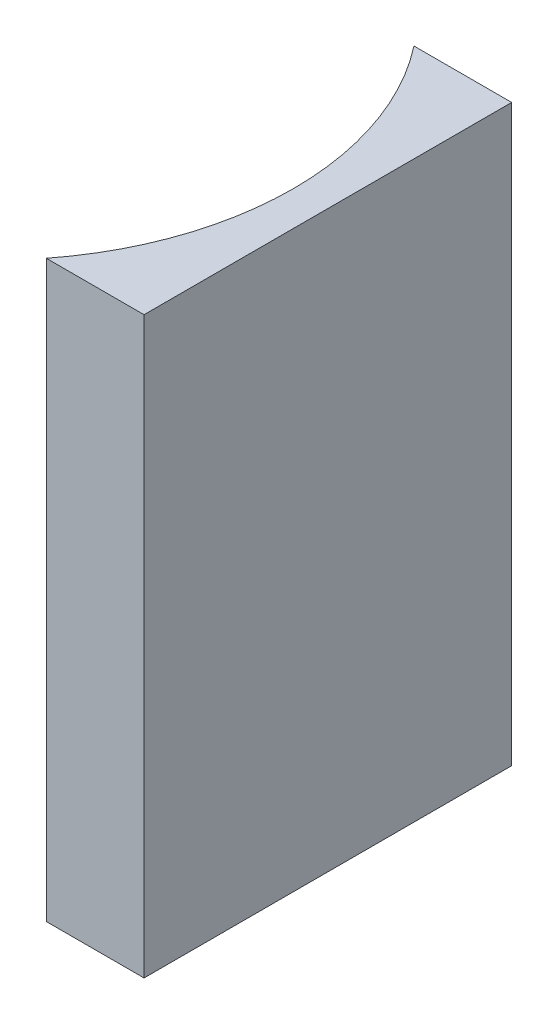
SolidWorks part; units mm, degrees
ref_plane "前视基准面" through (0, 0, 0) normal (0, 0, 1) x (1, 0, 0)
ref_plane "上视基准面" through (0, 0, 0) normal (0, 1, 0) x (1, 0, 0)
ref_plane "右视基准面" through (0, 0, 0) normal (1, 0, 0) x (0, 0, -1)
sketch "草图1" plane through (0, 0, 0) normal (0, 1, 0) x (1, 0, 0)
  line L0 (0, 0) -> (0, -16)
  line L1 (0, 0) -> (-4.253, 0)
  line L2 (0, -16) -> (-4.253, -16)
  line L3 (8.2336, -8) -> (-10.4405, -8) construction
  arc A0 (-4.253, -16) -> (-4.253, 0) centre (-14.5, -8) ccw
  point P7 (-1.5, -8)
  point P8 (0, -8)
  dimension "D2" = 13
  dimension "D3" = 1.5
  dimension "D1" = 16
extrude "凸台-拉伸1" add sketch "草图1" along normal blind 25
